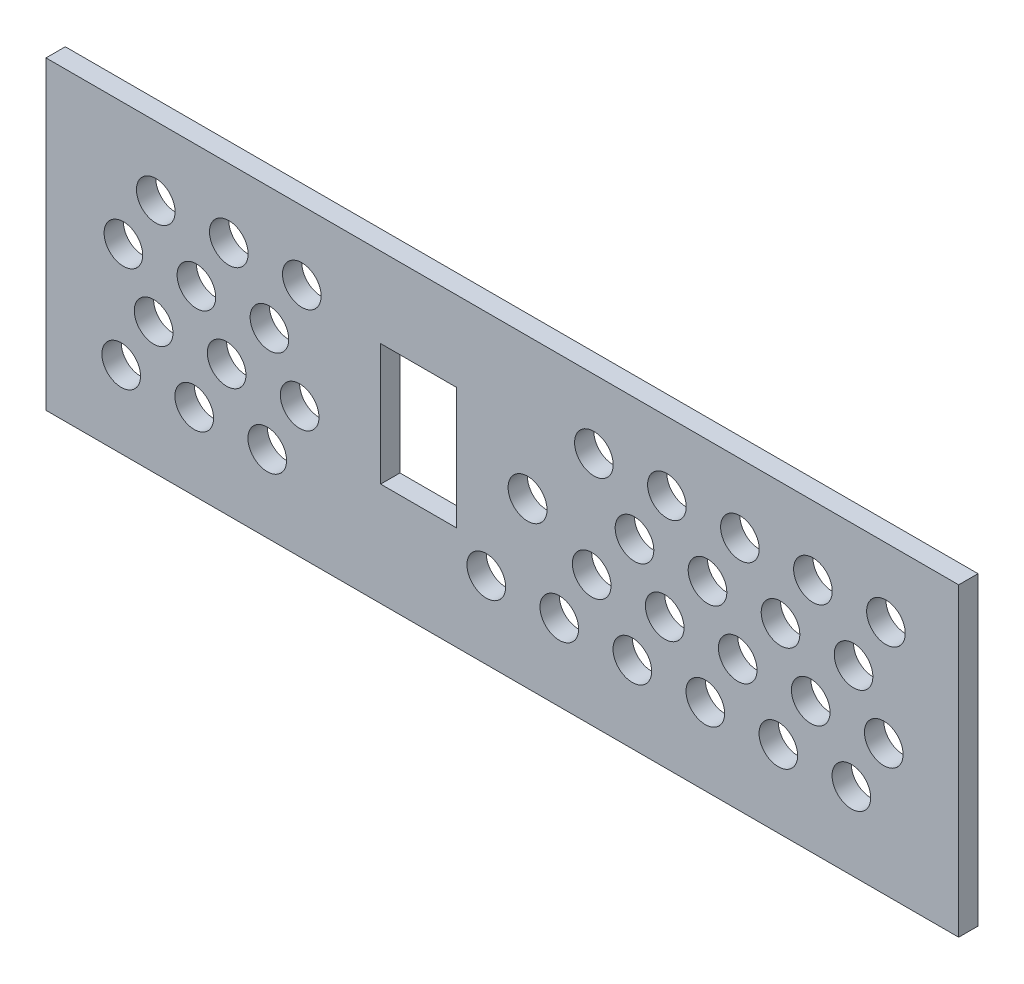
SolidWorks part; units mm, degrees
ref_plane "Front Plane" through (0, 0, 0) normal (0, 0, 1) x (1, 0, 0)
ref_plane "Top Plane" through (0, 0, 0) normal (0, 1, 0) x (1, 0, 0)
ref_plane "Right Plane" through (0, 0, 0) normal (1, 0, 0) x (0, 0, -1)
sketch "Sketch1" plane through (0, 0, 0) normal (0, 0, 1) x (1, 0, 0)
  line L16 (-7.5, 11) -> (-20, 11)
  line L17 (-7.5, -9) -> (-7.5, 11)
  line L18 (-20, -9) -> (-7.5, -9)
  line L19 (-20, 11) -> (-20, -9)
  line L32 (57.6937, -13.75) -> (57.6937, -24)
  line L33 (57.6937, -24) -> (73, -24)
  line L34 (73, -24) -> (73, -10.75)
  line L35 (73, -10.75) -> (53.0981, -10.75)
  line L36 (53.0981, -10.75) -> (53.0981, -13.75)
  line L37 (53.0981, -13.75) -> (57.6937, -13.75)
  line L38 (53.0981, 13.25) -> (73, 13.25)
  line L39 (73, 13.25) -> (73, 24)
  line L40 (73, 24) -> (57.6937, 24)
  line L41 (57.6937, 24) -> (57.6937, 16.25)
  line L42 (57.6937, 16.25) -> (53.0981, 16.25)
  line L43 (53.0981, 16.25) -> (53.0981, 13.25)
  line L44 (-73, -10.75) -> (-73, -24)
  line L45 (-73, -24) -> (-57.6937, -24)
  line L46 (-57.6937, -24) -> (-57.6937, -13.75)
  line L47 (-57.6937, -13.75) -> (-53.0981, -13.75)
  line L48 (-53.0981, -13.75) -> (-53.0981, -10.75)
  line L49 (-53.0981, -10.75) -> (-73, -10.75)
  line L50 (-57.6937, 24) -> (-73, 24)
  line L51 (-73, 24) -> (-73, 13.25)
  line L52 (-73, 13.25) -> (-53.0981, 13.25)
  line L53 (-53.0981, 13.25) -> (-53.0981, 16.25)
  line L54 (-53.0981, 16.25) -> (-57.6937, 16.25)
  line L55 (-57.6937, 16.25) -> (-57.6937, 24)
  line L56 (-43.3063, -13.75) -> (-43.3063, -24)
  line L57 (-43.3063, -24) -> (43.3063, -24)
  line L58 (43.3063, -24) -> (43.3063, -13.75)
  line L59 (43.3063, -13.75) -> (47.9019, -13.75)
  line L60 (47.9019, -13.75) -> (47.9019, -6.75)
  line L61 (47.9019, -6.75) -> (47.3377, -6.75)
  line L62 (47.3377, -6.75) -> (47.3377, 9.25)
  line L63 (47.3377, 9.25) -> (47.9019, 9.25)
  line L64 (47.9019, 9.25) -> (47.9019, 16.25)
  line L65 (47.9019, 16.25) -> (43.3063, 16.25)
  line L66 (43.3063, 16.25) -> (43.3063, 24)
  line L67 (43.3063, 24) -> (-43.3063, 24)
  line L68 (-43.3063, 24) -> (-43.3063, 16.25)
  line L69 (-43.3063, 16.25) -> (-47.9019, 16.25)
  line L70 (-47.9019, 16.25) -> (-47.9019, 9.25)
  line L71 (-47.9019, 9.25) -> (-47.3377, 9.25)
  line L72 (-47.3377, 9.25) -> (-47.3377, -6.75)
  line L73 (-47.3377, -6.75) -> (-47.9019, -6.75)
  line L74 (-47.9019, -6.75) -> (-47.9019, -13.75)
  line L75 (-47.9019, -13.75) -> (-43.3063, -13.75)
  circle A0 centre (4.144, 1) radius 3.2
extrude "Boss-Extrude1" add sketch "Sketch1" along normal blind 3.175
sketch "Sketch2" plane through (0, 0, 3.175) normal (0, 0, 1) x (1, 0, 0)
  line L0 (-43.3063, -24) -> (43.3063, -24) construction
  line L1 (-73, 24) -> (-29.7328, 24)
  line L2 (-73, 24) -> (-73, -24)
  line L3 (-73, -24) -> (-29.7328, -24)
  line L4 (-29.7328, 24) -> (-29.7328, -24)
  line L6 (73, 24) -> (36.5119, 24)
  line L7 (73, 24) -> (73, -24)
  line L8 (73, -24) -> (36.5119, -24)
  line L9 (36.5119, 24) -> (36.5119, -24)
extrude "Boss-Extrude2" add sketch "Sketch2" against normal blind 3.175
sketch "Sketch3" plane through (0, 0, 3.175) normal (0, 0, 1) x (1, 0, 0)
  line L1 (-73, 24) -> (73, 24)
  line L2 (-73, 24) -> (-73, -24)
  line L3 (-73, -24) -> (73, -24)
  line L4 (73, 24) -> (73, -24)
  line L5 (-75, 24.1649) -> (75, 24.1649)
  line L6 (-75, 24.1649) -> (-75, -26)
  line L7 (-75, -26) -> (75, -26)
  line L8 (75, 24.1649) -> (75, -26)
  dimension "D1" = 2
  dimension "D2" = 2
  dimension "D3" = 2
extrude "Boss-Extrude3" add sketch "Sketch3" against normal blind 3.175
sketch "Sketch4" plane through (0, 0, 3.175) normal (0, 0, 1) x (1, 0, 0)
  circle A1 centre (-56.9558, 12.8578) radius 3.175
  circle A2 centre (-44.9558, 12.8578) radius 3.175
  circle A3 centre (-32.9558, 12.8578) radius 3.175
  circle A7 centre (15.0442, 12.8578) radius 3.175
  circle A8 centre (27.0442, 12.8578) radius 3.175
  circle A9 centre (39.0442, 12.8578) radius 3.175
  circle A10 centre (51.0442, 12.8578) radius 3.175
  circle A11 centre (63.0442, 12.8578) radius 3.175
  circle A12 centre (-62.2807, 4.035) radius 3.175
  circle A13 centre (-50.2807, 4.035) radius 3.175
  circle A14 centre (-38.2807, 4.035) radius 3.175
  circle A19 centre (21.7193, 4.035) radius 3.175
  circle A20 centre (33.7193, 4.035) radius 3.175
  circle A21 centre (45.7193, 4.035) radius 3.175
  circle A22 centre (57.7193, 4.035) radius 3.175
  circle A25 centre (-57.3126, -4.5516) radius 3.175
  circle A26 centre (-45.3126, -4.5516) radius 3.175
  circle A27 centre (-33.3126, -4.5516) radius 3.175
  circle A31 centre (14.6874, -4.5516) radius 3.175
  circle A32 centre (26.6874, -4.5516) radius 3.175
  circle A33 centre (38.6874, -4.5516) radius 3.175
  circle A34 centre (50.6874, -4.5516) radius 3.175
  circle A35 centre (62.6874, -4.5516) radius 3.175
  circle A36 centre (-62.6376, -13.3744) radius 3.175
  circle A37 centre (-50.6376, -13.3744) radius 3.175
  circle A38 centre (-38.6376, -13.3744) radius 3.175
  circle A41 centre (-2.6376, -13.3744) radius 3.175
  circle A42 centre (9.3624, -13.3744) radius 3.175
  circle A43 centre (21.3624, -13.3744) radius 3.175
  circle A44 centre (33.3624, -13.3744) radius 3.175
  circle A45 centre (45.3624, -13.3744) radius 3.175
  circle A46 centre (57.3624, -13.3744) radius 3.175
extrude "Cut-Extrude1" cut sketch "Sketch4" against normal blind 3.175
